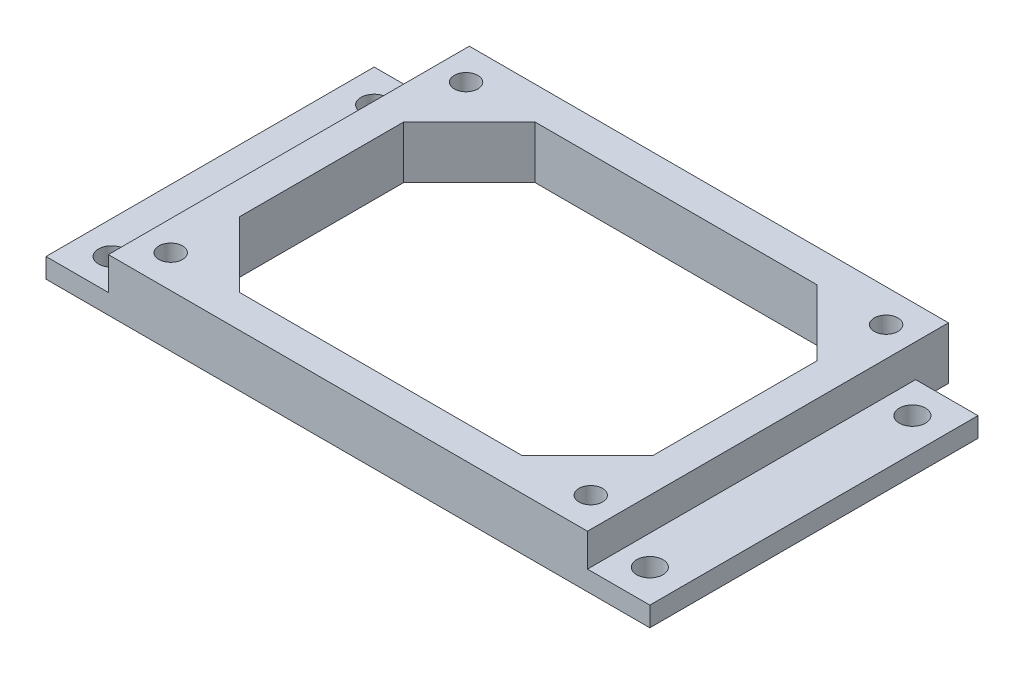
SolidWorks part; units mm, degrees
ref_plane "Front Plane" through (0, 0, 0) normal (0, 0, 1) x (1, 0, 0)
ref_plane "Top Plane" through (0, 0, 0) normal (0, 1, 0) x (1, 0, 0)
ref_plane "Right Plane" through (0, 0, 0) normal (1, 0, 0) x (0, 0, -1)
sketch "Sketch1" plane through (0, 0, 0) normal (0, 1, 0) x (1, 0, 0)
  line L1 (-36.5, -25) -> (36.5, -25)
  line L2 (-36.5, -25) -> (-36.5, 25)
  line L3 (-36.5, 25) -> (36.5, 25)
  line L4 (36.5, -25) -> (36.5, 25)
  line L5 (-36.5, -25) -> (36.5, 25) construction
  line L6 (-36.5, 25) -> (36.5, -25) construction
  point P0 (0, 0)
  dimension "D1" = 73
  dimension "D2" = 50
extrude "Boss-Extrude1" add sketch "Sketch1" along normal blind 5
sketch "Sketch2" plane through (0, 0, 0) normal (0, -1, 0) x (1, 0, 0)
  line L0 (-36.5, 25) -> (36.5, 25) construction
  line L1 (-46, -25) -> (46, -25)
  line L2 (-46, -25) -> (-46, 25)
  line L3 (-46, 25) -> (46, 25)
  line L4 (46, -25) -> (46, 25)
  line L5 (-46, -25) -> (46, 25) construction
  line L6 (-46, 25) -> (46, -25) construction
  point P0 (0, 0)
  dimension "D1" = 92
extrude "Boss-Extrude2" add sketch "Sketch2" along normal blind 3
sketch "Sketch3" plane through (0, 0, 0) normal (0, 1, 0) x (1, 0, 0)
  line L1 (-40.5, -15.25) -> (40.5, -15.25)
  line L2 (-40.5, -15.25) -> (-40.5, 15.25)
  line L3 (-40.5, 15.25) -> (40.5, 15.25)
  line L4 (40.5, -15.25) -> (40.5, 15.25)
  line L5 (-40.5, -15.25) -> (40.5, 15.25) construction
  line L6 (-40.5, 15.25) -> (40.5, -15.25) construction
  point P0 (0, 0)
  dimension "D1" = 30.5
  dimension "D2" = 81
hole_wizard "M3 Clearance Hole1" positions "Sketch7" profile "Sketch8" hole size "M3" standard "ANSI Metric"
sketch "Sketch7" plane through (0, 0, 0) normal (0, 1, 0) x (1, 0, 0)
  line L0 (-46, 25) -> (-36.5, 25) construction
  line L1 (36.5, 25) -> (46, 25) construction
  line L2 (46, -25) -> (36.5, -25) construction
  line L3 (-36.5, -25) -> (-46, -25) construction
  line L4 (-46, -25) -> (-46, 25) construction
  line L5 (46, 25) -> (46, -25) construction
  point P0 (-41, 20)
  point P2 (-41, -20)
  point P4 (41, 20)
  point P6 (41, -20)
  dimension "D1" = 5
  dimension "D2" = 5
  dimension "D3" = 5
  dimension "D4" = 5
  dimension "D5" = 5
  dimension "D6" = 5
sketch "Sketch8" plane through (-41, 0, -20) normal (1, 0, 0) x (0, 0, 1)
  line L0 (0, 0) -> (0, 11.2017)
  line L1 (0, 11.2017) -> (2, 10)
  line L2 (2, 10) -> (2, 0)
  line L5 (2, 0) -> (0, 0)
  line L10 (0, 11.2017) -> (-2, 10) construction
  line L11 (0, -6.35) -> (0, 107.95) construction
  dimension "Hole Dia." = 4
  dimension "Hole Depth" = 10
  dimension "Drill Angle" = 118
sketch "Sketch9" plane through (0, 0, -25) normal (0, 0, -1) x (-1, 0, 0)
  line L0 (-36.5, 5) -> (36.5, 5) construction
  line L1 (-36.5, 5) -> (36.5, 5)
  line L2 (-36.5, 5) -> (-36.5, -3)
  line L3 (-36.5, -3) -> (36.5, -3)
  line L4 (36.5, 5) -> (36.5, -3)
  line L5 (46, -3) -> (-46, -3) construction
  line L6 (-36.5, 5) -> (-36.5, 0) construction
  line L7 (36.5, 5) -> (36.5, 0) construction
extrude "Boss-Extrude3" add sketch "Sketch9" along normal blind 5
hole_wizard "M3 Clearance Hole3" positions "Sketch10" profile "Sketch11" hole size "M3" standard "ANSI Metric"
sketch "Sketch10" plane through (0, 5, 0) normal (0, 1, 0) x (1, 0, 0)
  line L1 (32, -20) -> (-32, -20)
  line L2 (32, -20) -> (32, 25)
  line L3 (32, 25) -> (-32, 25)
  line L4 (-32, -20) -> (-32, 25)
  line L5 (-36.5, -25) -> (36.5, -25) construction
  point P1 (32, -20)
  point P2 (-32, 25)
  point P57 (32, 25)
  point P58 (-32, -20)
  point P60 (0, -20)
  point P63 (0, -25)
  dimension "D1" = 64
  dimension "D2" = 45
  dimension "D3" = 5
sketch "Sketch11" plane through (32, 5, 20) normal (1, 0, 0) x (0, 0, 1)
  line L0 (0, 0) -> (0, 11.0815)
  line L1 (0, 11.0815) -> (1.8, 10)
  line L2 (1.8, 10) -> (1.8, 0)
  line L5 (1.8, 0) -> (0, 0)
  line L10 (0, 11.0815) -> (-1.8, 10) construction
  line L11 (0, -6.35) -> (0, 107.95) construction
  dimension "Hole Dia." = 3.6
  dimension "Hole Depth" = 10
  dimension "Drill Angle" = 118
sketch "Sketch12" plane through (0, 5, 0) normal (0, 1, 0) x (1, 0, 0)
  line L4 (21.5, -20) -> (31.5, -10)
  line L5 (-31.5, -10) -> (-21.5, -20)
  line L6 (31.5, 15) -> (21.5, 25)
  line L7 (-21.5, 25) -> (-31.5, 15)
  line L8 (31.5, -20) -> (31.5, 25)
  line L9 (31.5, 25) -> (-31.5, 25)
  line L10 (-31.5, 25) -> (-31.5, -20)
  line L11 (-31.5, -20) -> (31.5, -20)
  line L12 (31.5, -10) -> (31.5, 15)
  line L13 (21.5, 25) -> (-21.5, 25)
  line L14 (-31.5, 15) -> (-31.5, -10)
  line L15 (-21.5, -20) -> (21.5, -20)
  dimension "D1" = 5
extrude "Cut-Extrude1" cut sketch "Sketch12" against normal through all
equation "\"8`\"=84.8464"
